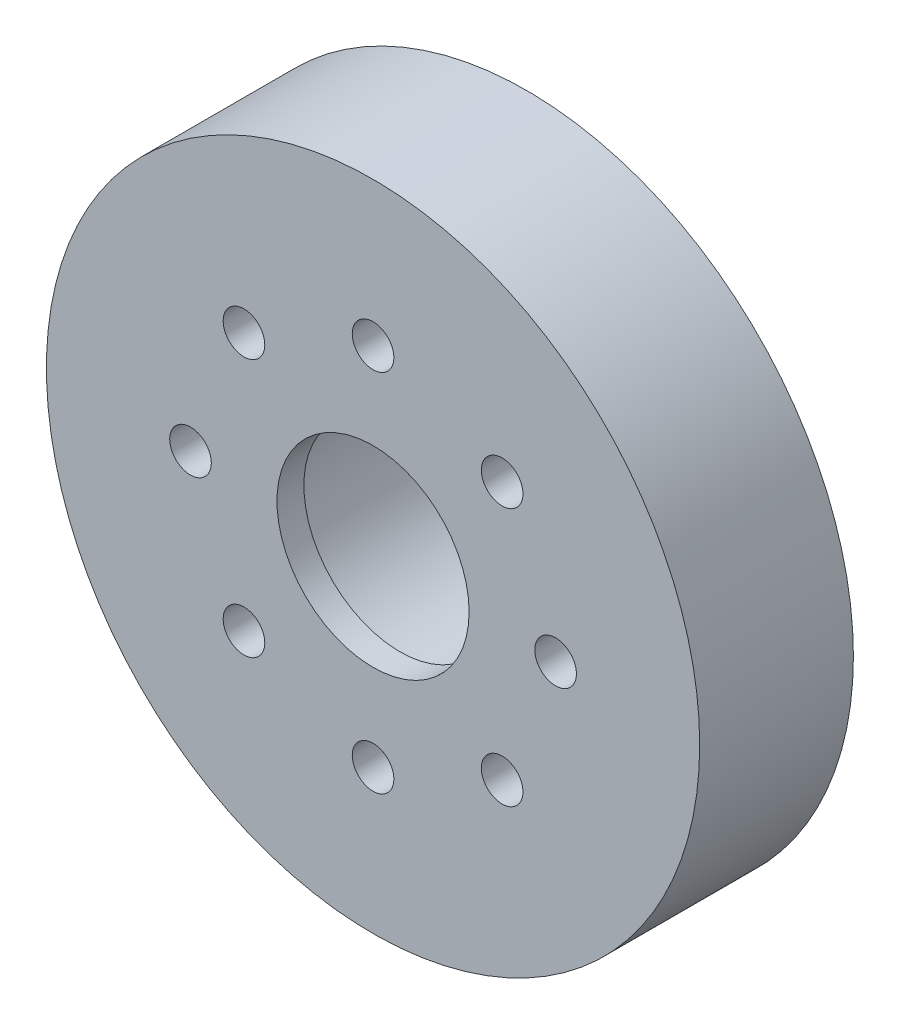
SolidWorks part; units mm, degrees
ref_plane "Front Plane" through (0, 0, 0) normal (0, 0, 1) x (1, 0, 0)
ref_plane "Top Plane" through (0, 0, 0) normal (0, 1, 0) x (1, 0, 0)
ref_plane "Right Plane" through (0, 0, 0) normal (1, 0, 0) x (0, 0, -1)
sketch "Sketch1" plane through (0, 0, 0) normal (0, 0, 1) x (1, 0, 0)
  circle A0 centre (0, 0) radius 43.18
  dimension "D1" = 86.36
extrude "Boss-Extrude1" add sketch "Sketch1" along normal blind 20.32
sketch "Sketch5" plane through (0, 0, 0) normal (0, 0, -1) x (-1, 0, 0)
  point P0 (0, 0)
sketch "Sketch6" plane through (0, 0, 0) normal (0, 0, -1) x (-1, 0, 0)
  circle A0 centre (0, 0) radius 29.21 construction
  circle A1 centre (0, 0) radius 24.13 construction
  point P5 (0, 24.13)
  dimension "D1" = 58.42
  dimension "D2" = 5.08
hole_wizard "1 NPT Tapped Hole2" positions "Sketch5" profile "Sketch7" size "1" standard "ANSI Inch" end condition up to next
sketch "Sketch7" plane through (0, 0, 0) normal (1, 0, 0) x (0, 1, 0)
  line L0 (0, 0) -> (0, 20.32)
  line L1 (0, 20.32) -> (14.4907, 20.32)
  line L2 (-15.228, 16.764) -> (-15.7299, 0) construction
  line L3 (14.4907, 20.32) -> (14.4907, 16.764)
  line L4 (14.4907, 16.764) -> (15.228, 16.764)
  line L5 (15.228, 16.764) -> (15.7299, 0)
  line L7 (15.7299, 0) -> (0, 0)
  line L8 (0, -6.35) -> (0, 107.95) construction
  line L11 (-14.4907, 16.764) -> (-15.228, 16.764) construction
  dimension "Thru Tap Drill Dia." = 28.9814
  dimension "Thru Tap Drill Depth" = 20.32
  dimension "Thread Dia." = 31.4598
  dimension "Thread Angle" = 3.43
  dimension "Thread Depth" = 16.764
cosmetic thread "Hole Thread1" parameters "D1"=16.764, "D2"=33.3988
hole_wizard "M5 Clearance Hole1" positions "Sketch6" profile "Sketch8" hole size "M5" standard "ANSI Metric" end condition up to next
sketch "Sketch8" plane through (0, 24.13, 0) normal (1, 0, 0) x (0, 1, 0)
  line L0 (0, 0) -> (0, 20.32)
  line L1 (0, 20.32) -> (2.75, 20.32)
  line L2 (2.75, 20.32) -> (2.75, 0)
  line L5 (2.75, 0) -> (0, 0)
  line L11 (0, -6.35) -> (0, 107.95) construction
  dimension "Thru Hole Dia." = 5.5
  dimension "Thru Hole Depth" = 20.32
pattern_circular "CirPattern1" count 8 every 45 about axis through (0, 0, 0) along (0, 0, 1) of "M5 Clearance Hole1"
sketch "Sketch9" plane through (0, 0, 20.32) normal (0, 0, 1) x (1, 0, 0)
  circle A0 centre (0, 0) radius 12.7
  circle A1 centre (0, 0) radius 14.4907 construction
  circle A2 centre (0, 0) radius 14.4907
  dimension "D1" = 25.4
extrude "Boss-Extrude2" add sketch "Sketch9" against normal up to surface (3.556 mm away) up to face at (-14.4907, 0, 16.764)
equation "\"cavity_depth\"=0.031in"
equation "\"Cavity_width\"=0.031in"
equation "\"tooth_width\"=0.01in"
equation "\"Flange_OD\"=2.3in"
equation "\"fitting_OD\"= 1.3in"
equation "\"plate_thick\"= .8in"
equation "\"D1@Boss-Extrude1\"=\"plate_thick\""
equation "\"D1@Sketch6\"=\"Flange_OD\""
equation "\"D1@Sketch1\"=\"IPS_flange_radius\"*2"
equation "\"bearing_radius\"= 0.629921"
equation "\"bearing_width\"=0.393701"
equation "\"kero_radius\"=0.334in"
equation "\"lox_radius\"=0.23622in"
equation "\"seal_step\"=0.01in"
equation "\"purge_length\"=0.04in"
equation "\"insert_radius\" = 0.6in"
equation "\"recycle_groove width\" = 0.06in"
equation "\"recycle_groove_depth\" = 0.06in"
equation "\"N2_purge_width\"= .06in"
equation "\"N2_purge_depth\"= .06in"
equation "\"drain_width\"= .06in"
equation "\"drain_depth\"= .06in"
equation "\"radial_clearance\"= .002in"
equation "\"IPS_flange_width\"= .4in"
equation "\"IPS_flange_radius\" = 1.7in"
equation "\"IPS_LOX_male_radius\"= .9in"
equation "\"IPS_Kero_male_radius\" = .9in"
equation "\"IPS_radius\"= 1.2in"
equation "\"InsertLength\"= 1in"
